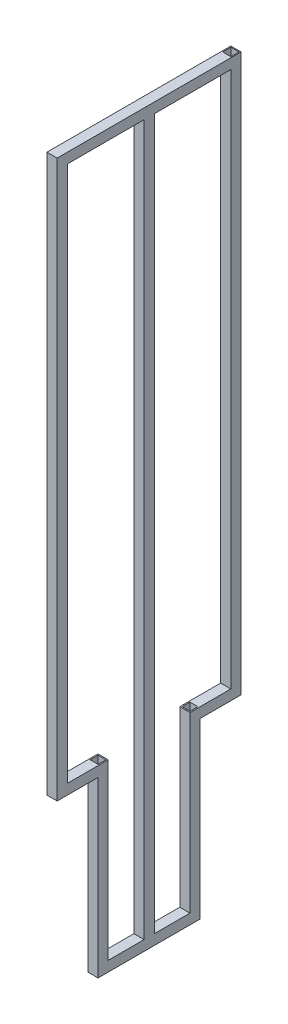
SolidWorks part; units mm, degrees
ref_plane "Front" through (0, 0, 0) normal (0, 0, 1) x (1, 0, 0)
ref_plane "Top" through (0, 0, 0) normal (0, 1, 0) x (1, 0, 0)
ref_plane "Right" through (0, 0, 0) normal (1, 0, 0) x (0, 0, -1)
sketch "Sketch1" plane through (0, 0, 0) normal (0, 1, 0) x (1, 0, 0)
  line L1 (-1, -1) -> (1, -1)
  line L2 (-1, -1) -> (-1, 1)
  line L3 (-1, 1) -> (1, 1)
  line L4 (1, -1) -> (1, 1)
  line L5 (-1, -1) -> (1, 1) construction
  line L6 (-1, 1) -> (1, -1) construction
  line L7 (-0.8, 0.8) -> (0.8, 0.8)
  line L8 (-0.8, 0.8) -> (-0.8, -0.8)
  line L9 (-0.8, -0.8) -> (0.8, -0.8)
  line L10 (0.8, 0.8) -> (0.8, -0.8)
  line L11 (-0.8, 0.8) -> (0.8, -0.8) construction
  line L12 (-0.8, -0.8) -> (0.8, 0.8) construction
  point P0 (0, 0)
  point P6 (0, 0)
  dimension "D1" = 2
  dimension "D2" = 2
  dimension "D3" = 0.2
  dimension "D4" = 0.2
extrude "Boss-Extrude1" add sketch "Sketch1" along normal blind 109
sketch "Sketch2" plane through (0, 0, 1) normal (0, 0, 1) x (1, 0, 0)
  line L1 (-1, 107) -> (1, 107)
  line L2 (-1, 107) -> (-1, 109)
  line L3 (-1, 109) -> (1, 109)
  line L4 (1, 107) -> (1, 109)
  line L5 (-1, 107) -> (1, 109) construction
  line L6 (-1, 109) -> (1, 107) construction
  line L7 (-0.8, 108.8) -> (0.8, 108.8)
  line L8 (-0.8, 108.8) -> (-0.8, 107.2)
  line L9 (-0.8, 107.2) -> (0.8, 107.2)
  line L10 (0.8, 108.8) -> (0.8, 107.2)
  line L11 (-0.8, 108.8) -> (0.8, 107.2) construction
  line L12 (-0.8, 107.2) -> (0.8, 108.8) construction
  point P0 (0, 108)
  point P6 (0, 108)
  dimension "D1" = 0.2
  dimension "D2" = 0.2
  dimension "D3" = 2
  dimension "D4" = 2
extrude "Boss-Extrude2" add sketch "Sketch2" along normal blind 34
ref_plane "Plane1" through (0, 0, 17) normal (0, 0, 1) x (1, 0, 0)
mirror "Mirror1" about plane through (0, 0, 17) normal (0, 0, 1) of "Boss-Extrude1"
sketch "Sketch3" plane through (0, 0, 1) normal (0, 0, 1) x (1, 0, 0)
  line L1 (1, 2) -> (-1, 2)
  line L2 (1, 2) -> (1, 0)
  line L3 (1, 0) -> (-1, 0)
  line L4 (-1, 2) -> (-1, 0)
  line L5 (1, 2) -> (-1, 0) construction
  line L6 (1, 0) -> (-1, 2) construction
  line L7 (0.8, 1.8) -> (-0.8, 1.8)
  line L8 (0.8, 1.8) -> (0.8, 0.2)
  line L9 (0.8, 0.2) -> (-0.8, 0.2)
  line L10 (-0.8, 1.8) -> (-0.8, 0.2)
  line L11 (0.8, 1.8) -> (-0.8, 0.2) construction
  line L12 (0.8, 0.2) -> (-0.8, 1.8) construction
  point P0 (0, 1)
  point P6 (0, 1)
  dimension "D1" = 2
  dimension "D2" = 0.2
extrude "Boss-Extrude3" add sketch "Sketch3" along normal blind 6
sketch "Sketch7" plane through (0, 2, 0) normal (0, 1, 0) x (1, 0, 0)
  line L1 (-1, -9) -> (1, -9)
  line L2 (-1, -9) -> (-1, -7)
  line L3 (-1, -7) -> (1, -7)
  line L4 (1, -9) -> (1, -7)
  line L5 (-1, -9) -> (1, -7) construction
  line L6 (-1, -7) -> (1, -9) construction
  line L7 (-0.77, -7.23) -> (0.77, -7.23)
  line L8 (-0.77, -7.23) -> (-0.77, -8.77)
  line L9 (-0.77, -8.77) -> (0.77, -8.77)
  line L10 (0.77, -7.23) -> (0.77, -8.77)
  line L11 (-0.77, -7.23) -> (0.77, -8.77) construction
  line L12 (-0.77, -8.77) -> (0.77, -7.23) construction
  point P0 (0, -8)
  point P6 (0, -8)
  dimension "D1" = 2
  dimension "D2" = 0.23
extrude "Boss-Extrude4" add sketch "Sketch7" against normal blind 36
mirror "Mirror2" about plane through (0, 0, 17) normal (0, 0, 1) of "Boss-Extrude4", "Boss-Extrude3"
sketch "Sketch8" plane through (0, 0, 25) normal (0, 0, -1) x (-1, 0, 0)
  line L1 (-1, -32) -> (1, -32)
  line L2 (-1, -32) -> (-1, -34)
  line L3 (-1, -34) -> (1, -34)
  line L4 (1, -32) -> (1, -34)
  line L5 (-1, -32) -> (1, -34) construction
  line L6 (-1, -34) -> (1, -32) construction
  line L7 (-0.8, -32.2) -> (0.8, -32.2)
  line L8 (-0.8, -32.2) -> (-0.8, -33.8)
  line L9 (-0.8, -33.8) -> (0.8, -33.8)
  line L10 (0.8, -32.2) -> (0.8, -33.8)
  line L11 (-0.8, -32.2) -> (0.8, -33.8) construction
  line L12 (-0.8, -33.8) -> (0.8, -32.2) construction
  point P0 (0, -33)
  point P6 (0, -33)
  dimension "D1" = 2
  dimension "D2" = 0.2
extrude "Boss-Extrude5" add sketch "Sketch8" along normal up to next
scale "Scale2" scale about origin uniform scaling yes scale factor 10
sketch "Sketch9" plane through (0, 1070, 0) normal (0, -1, 0) x (1, 0, 0)
  line L0 (-10, 330) -> (-10, 10) construction
  line L1 (10, 179.7381) -> (-10, 179.7381)
  line L2 (10, 179.7381) -> (10, 159.7381)
  line L3 (10, 159.7381) -> (-10, 159.7381)
  line L4 (-10, 179.7381) -> (-10, 159.7381)
  line L5 (10, 179.7381) -> (-10, 159.7381) construction
  line L6 (10, 159.7381) -> (-10, 179.7381) construction
  line L8 (8, 177.7381) -> (-8, 177.7381)
  line L9 (8, 177.7381) -> (8, 161.7381)
  line L10 (8, 161.7381) -> (-8, 161.7381)
  line L11 (-8, 177.7381) -> (-8, 161.7381)
  line L12 (8, 177.7381) -> (-8, 161.7381) construction
  line L13 (8, 161.7381) -> (-8, 177.7381) construction
  point P0 (0, 169.7381)
  point P7 (0, 169.7381)
  dimension "D1" = 20
  dimension "D2" = 2
extrude "Boss-Extrude6" add sketch "Sketch9" along normal up to next
